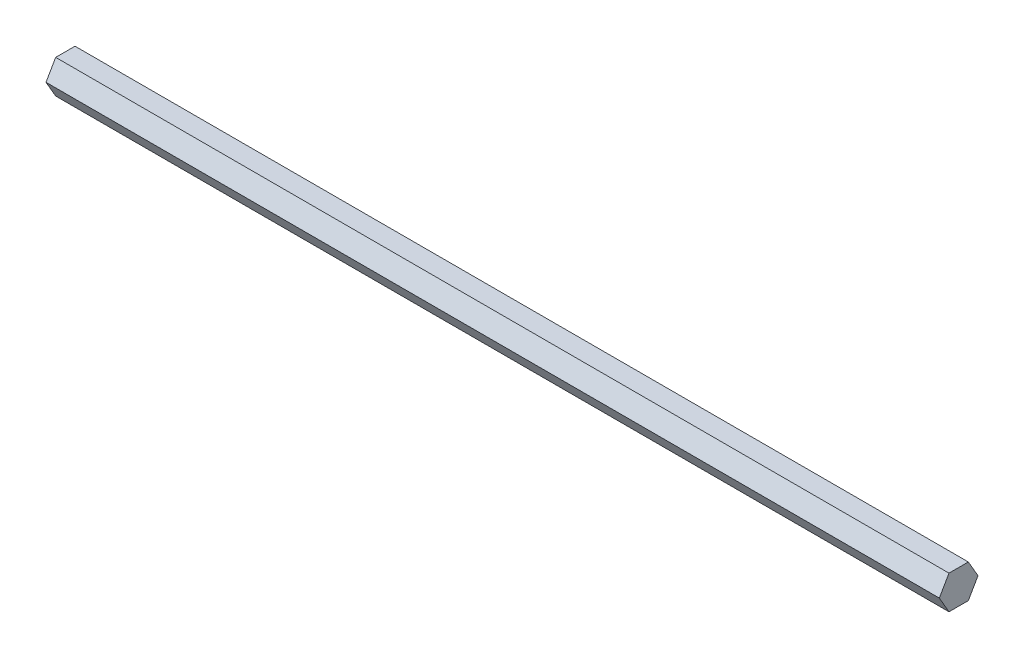
SolidWorks part; units mm, degrees
ref_plane "Front" through (0, 0, 0) normal (0, 0, 1) x (1, 0, 0)
ref_plane "Top" through (0, 0, 0) normal (0, 1, 0) x (1, 0, 0)
ref_plane "Right" through (0, 0, 0) normal (1, 0, 0) x (0, 0, -1)
sketch "Sketch1" plane through (0, 0, 0) normal (1, 0, 0) x (0, 0, -1)
  line L1 (2.7496, -4.7625) -> (5.4993, 0)
  line L2 (5.4993, 0) -> (2.7496, 4.7625)
  line L3 (2.7496, 4.7625) -> (-2.7496, 4.7625)
  line L4 (-2.7496, 4.7625) -> (-5.4993, 0)
  line L5 (-5.4993, 0) -> (-2.7496, -4.7625)
  line L6 (-2.7496, -4.7625) -> (2.7496, -4.7625)
  circle A0 centre (0, 0) radius 4.7625 construction
  dimension "D1" = 9.525
extrude "Boss-Extrude1" add sketch "Sketch1" along normal mid plane 254
